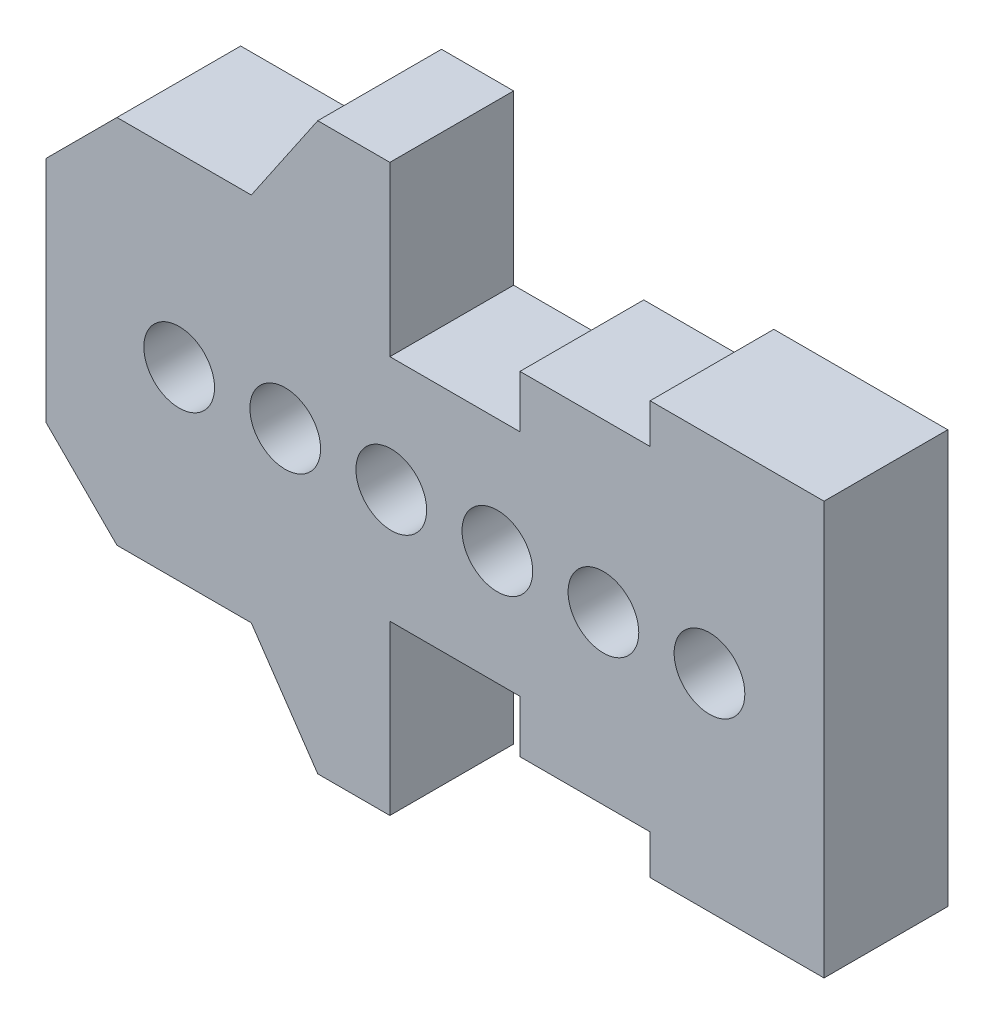
SolidWorks part; units mm, degrees
ref_plane "Front Plane" through (0, 0, 0) normal (0, 0, 1) x (1, 0, 0)
ref_plane "Top Plane" through (0, 0, 0) normal (0, 1, 0) x (1, 0, 0)
ref_plane "Right Plane" through (0, 0, 0) normal (1, 0, 0) x (0, 0, -1)
sketch "Sketch4" plane through (0, 0, 0) normal (0, 0, 1) x (1, 0, 0)
  line L22 (-66.6654, 20.7284) -> (-66.6654, -20.4196)
  line L23 (-66.6654, -20.4196) -> (-53.9654, -33.1196)
  line L24 (-53.9654, -33.1196) -> (-29.8354, -33.1196)
  line L25 (-29.8354, -33.1196) -> (-17.8974, -50.6456)
  line L26 (-17.8974, -50.6456) -> (-4.9434, -50.6456)
  line L27 (-4.9434, -50.6456) -> (-4.9434, -20.4196)
  line L28 (-4.9434, -20.4196) -> (18.4246, -20.4196)
  line L29 (18.4246, -20.4196) -> (18.4246, -29.8176)
  line L30 (18.4246, -29.8176) -> (41.7926, -29.8176)
  line L31 (41.7926, -29.8176) -> (41.7926, -36.9296)
  line L32 (41.7926, -36.9296) -> (73.0346, -36.9296)
  line L33 (73.0346, -36.9296) -> (73.0346, 37.2384)
  line L34 (73.0346, 0.1544) -> (-66.6654, 0.1544)
  line L36 (41.7926, 37.2384) -> (73.0346, 37.2384)
  line L37 (41.7926, 30.1264) -> (41.7926, 37.2384)
  line L38 (18.4246, 30.1264) -> (41.7926, 30.1264)
  line L39 (18.4246, 20.7284) -> (18.4246, 30.1264)
  line L40 (-4.9434, 20.7284) -> (18.4246, 20.7284)
  line L41 (-4.9434, 50.9544) -> (-4.9434, 20.7284)
  line L42 (-17.8974, 50.9544) -> (-4.9434, 50.9544)
  line L43 (-29.8354, 33.4284) -> (-17.8974, 50.9544)
  line L44 (-53.9654, 33.4284) -> (-29.8354, 33.4284)
  line L45 (-66.6654, 20.7284) -> (-53.9654, 33.4284)
  circle A1 centre (-42.7894, 0.1544) radius 6.35
  circle A2 centre (-23.7394, 0.1544) radius 6.35
  circle A3 centre (-4.6894, 0.1544) radius 6.35
  circle A4 centre (14.3606, 0.1544) radius 6.35
  circle A5 centre (33.4106, 0.1544) radius 6.35
  circle A6 centre (52.4606, 0.1544) radius 6.35
  point P25 (-60.3154, -26.7696)
  dimension "D14" = 12.7
  dimension "D1" = 61.722
  dimension "D2" = 85.09
  dimension "D3" = 48.768
  dimension "D4" = 108.458
  dimension "D5" = 36.83
  dimension "D6" = 17.526
  dimension "D7" = 139.7
  dimension "D8" = 20.574
  dimension "D9" = 33.274
  dimension "D10" = 12.7
  dimension "D11" = 7.112
  dimension "D12" = 16.51
  dimension "D13" = 37.084
  dimension "D15" = 23.876
  dimension "D16" = 6
extrude "Boss-Extrude1" add sketch "Sketch4" along normal blind 22.225 contours A6 L34 A5 A4 A3 A2 A1 L22 L23 L24 L25 L26 L27 L28 L29 L30 L31 L32 L33 | A6 L34 L33 L36 L37 L38 L39 L40 L41 L42 L43 L44 L45 L22 A1 A2 A3 A4 A5
